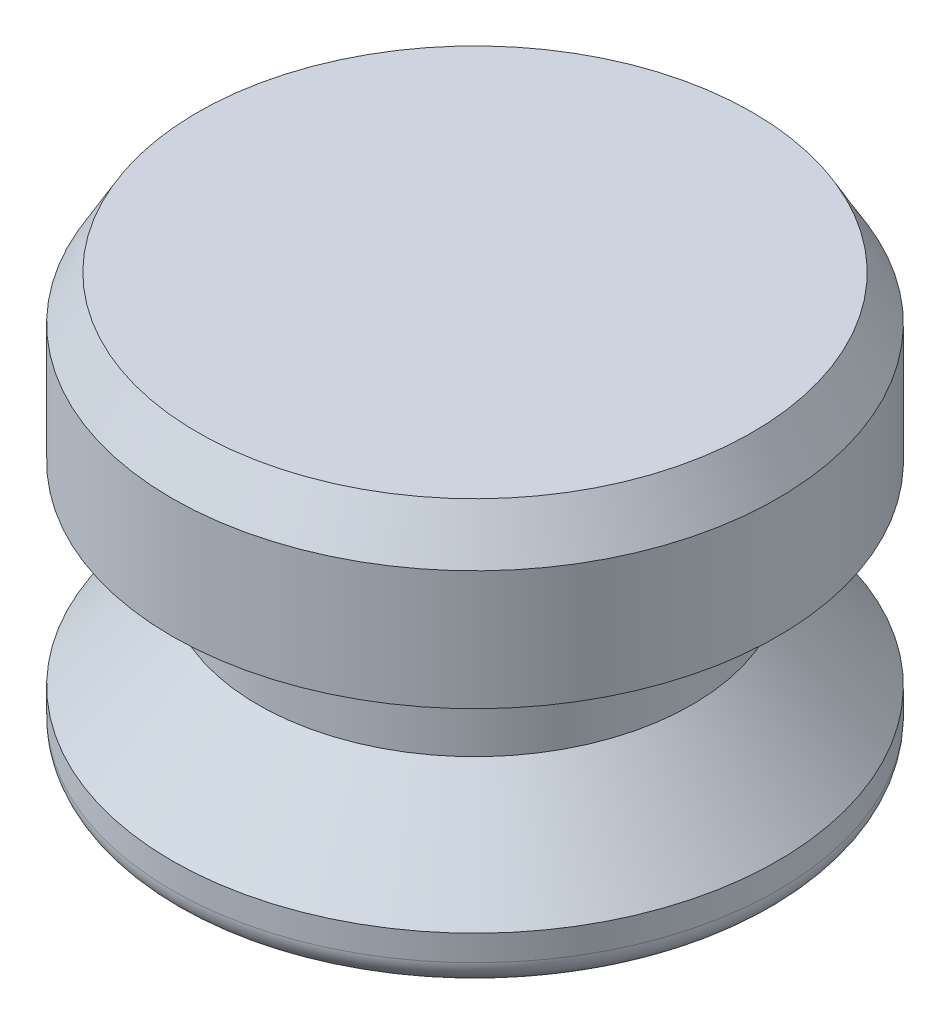
SolidWorks part; units mm, degrees
ref_plane "Front Plane" through (0, 0, 0) normal (0, 0, 1) x (1, 0, 0)
ref_plane "Top Plane" through (0, 0, 0) normal (0, 1, 0) x (1, 0, 0)
ref_plane "Right Plane" through (0, 0, 0) normal (1, 0, 0) x (0, 0, -1)
sketch "Sketch1" plane through (0, 0, 0) normal (0, 0, 1) x (1, 0, 0)
  line L0 (0, 0) -> (0, 12.7) construction
  line L1 (0, 0) -> (-9.398, 0)
  line L2 (-9.398, 0) -> (-9.398, 1.5875)
  line L4 (-6.731, 4.445) -> (-6.731, 7.62)
  line L5 (-6.731, 7.62) -> (-9.398, 7.62)
  line L6 (-9.398, 7.62) -> (-9.398, 12.7)
  line L7 (-9.398, 12.7) -> (0, 12.7)
  line L8 (-9.525, 16.6801) -> (-9.525, -9.6051) construction
  line L9 (0, 0) -> (0, 12.7)
  line L10 (-6.731, 4.445) -> (-9.398, 1.5875)
  dimension "D1" = 12.7
  dimension "D2" = 9.398
  dimension "D3" = 3.175
  dimension "D4" = 1.5875
  dimension "D5" = 9.525
  dimension "D6" = 6.731
  dimension "D7" = 7.62
revolve "Revolve1" add sketch "Sketch1" angle 360 about L9
fillet "Fillet1" radius 0.7937 1 edges at (0, 0, -9.398)
chamfer "Chamfer1" distance 0.7937 angle 60 1 edges at (0, 12.7, -9.398)
